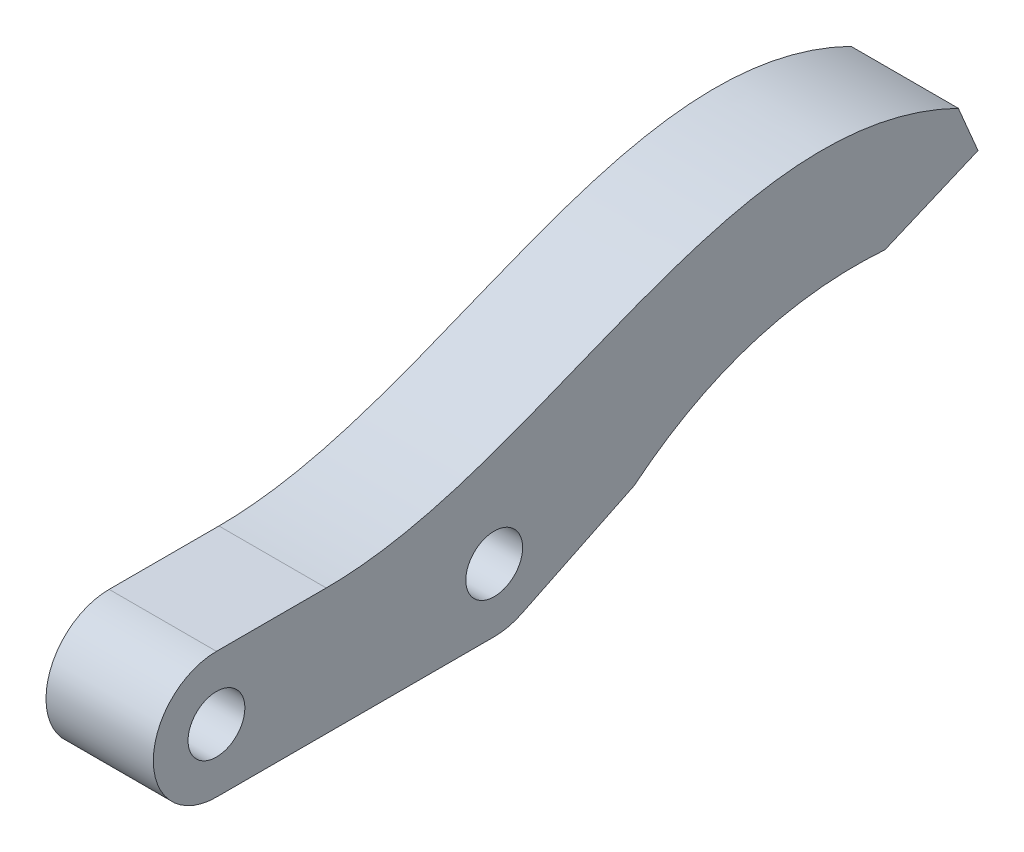
SolidWorks part; units mm, degrees
ref_plane "Front Plane" through (0, 0, 0) normal (0, 0, 1) x (1, 0, 0)
ref_plane "Top Plane" through (0, 0, 0) normal (0, 1, 0) x (1, 0, 0)
ref_plane "Right Plane" through (0, 0, 0) normal (1, 0, 0) x (0, 0, -1)
sketch "Sketch1" plane through (0, 0, 0) normal (1, 0, 0) x (0, 0, -1)
  line L1 (0, 0) -> (27, 0)
  line L2 (0, 0) -> (0, 10)
  line L3 (0, 10) -> (27, 10)
  circle A0 centre (5, 5) radius 2.25
  circle A1 centre (5, 5) radius 5
  circle A2 centre (27, 5) radius 5
  circle A3 centre (27, 5) radius 2.25
  dimension "D7" = 4.5
  dimension "D11" = 10
  dimension "D2" = 4.5
  dimension "D1" = 10
  dimension "D8" = 5
  dimension "D9" = 5
  dimension "D10" = 22
extrude "Boss-Extrude1" add sketch "Sketch1" along normal blind 8.5 contours A1 A0 | A2 L3 A1 L1 | A2 A3 | L2 A1 | L1 A1
sketch "Sketch2" plane through (8.5, 0, 0) normal (1, 0, 0) x (0, 0, -1)
  line L6 (5, 10) -> (27, 10) construction
  line L14 (5, 10) -> (27, 10)
  line L20 (29.1838, 0.5021) -> (38.0854, 4.8241)
  line L21 (57.948, 11.0678) -> (65.3138, 14.1895)
  line L22 (65.3138, 14.1895) -> (63.753, 17.8724)
  arc A3 (27, 0) -> (27, 10) centre (27, 5) ccw construction
  arc A4 (27, 0) -> (27, 10) centre (27, 5) ccw
  spline S0 degree 2 poles (38.0854, 4.8241) (46.7975, 11.8952) (57.948, 11.0678) knots 0 0 0 1 1 1
  spline S1 degree 3 poles (63.753, 17.8724) (45.9289, 26.5638) (31.0593, 10) (13.695, 10) knots 0 0 0 0 1 1 1 1
  point P2 (27, 5)
  dimension "D3" = 4
  dimension "D4" = 8
extrude "Boss-Extrude2" add sketch "Sketch2" against normal blind 8.5
